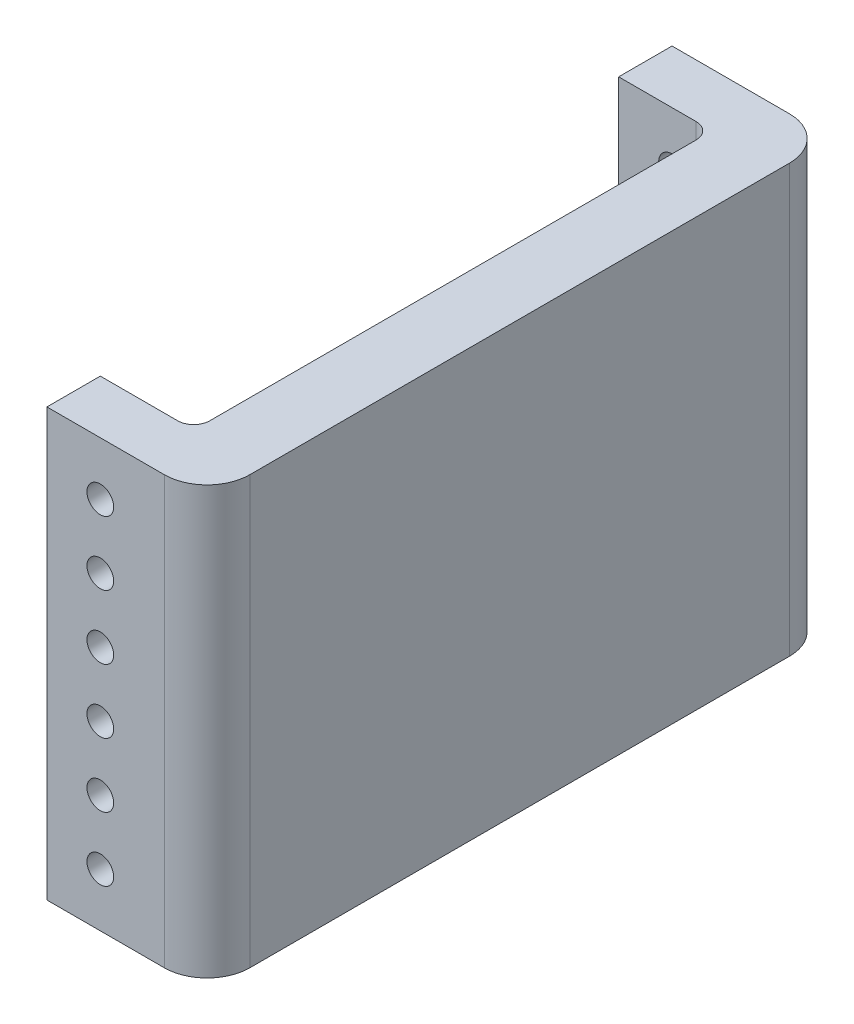
SolidWorks part; units mm, degrees
ref_plane "Front Plane" through (0, 0, 0) normal (0, 0, 1) x (1, 0, 0)
ref_plane "Top Plane" through (0, 0, 0) normal (0, 1, 0) x (1, 0, 0)
ref_plane "Right Plane" through (0, 0, 0) normal (1, 0, 0) x (0, 0, -1)
sketch "Sketch1" plane through (0, 0, 0) normal (1, 0, 0) x (0, 0, -1)
  line L1 (-837.5115, 764.4576) -> (-540.0775, 764.4576)
  line L2 (-837.5115, 764.4576) -> (-837.5115, 561.2576)
  line L3 (-837.5115, 561.2576) -> (-540.0775, 561.2576)
  line L4 (-540.0775, 764.4576) -> (-540.0775, 561.2576)
  dimension "D1" = 297.434
  dimension "D2" = 203.2
extrude "Boss-Extrude1" add sketch "Sketch1" along normal blind 76.2
sketch "Sketch3" plane through (0, 764.4576, 0) normal (0, 1, 0) x (1, 0, 0)
  line L0 (0, -540.0775) -> (0, -837.5115) construction
  line L1 (0, -565.4775) -> (44.45, -565.4775)
  line L2 (0, -565.4775) -> (0, -812.1115)
  line L3 (0, -812.1115) -> (44.45, -812.1115)
  line L4 (44.45, -565.4775) -> (44.45, -812.1115)
  line L5 (76.2, -540.0775) -> (0, -540.0775) construction
  line L6 (76.2, -837.5115) -> (0, -837.5115) construction
  line L7 (76.2, -540.0775) -> (76.2, -837.5115) construction
  dimension "D1" = 25.4
  dimension "D2" = 25.4
  dimension "D3" = 31.75
extrude "Cut-Extrude1" cut sketch "Sketch3" against normal through all
sketch "Sketch4" plane through (0, 0, 837.5115) normal (0, 0, 1) x (1, 0, 0)
  line L0 (76.2, 764.4576) -> (0, 764.4576) construction
  line L1 (0, 764.4576) -> (0, 561.2576) construction
  circle A0 centre (25.4, 739.0576) radius 6.35
  circle A1 centre (25.4, 708.5776) radius 6.35
  circle A2 centre (25.4, 678.0976) radius 6.35
  circle A3 centre (25.4, 647.6176) radius 6.35
  circle A4 centre (25.4, 617.1376) radius 6.35
  circle A5 centre (25.4, 586.6576) radius 6.35
  dimension "D1" = 25.4
  dimension "D2" = 25.4
extrude "Cut-Extrude2" cut sketch "Sketch4" against normal through all
fillet "Fillet1" radius 20.32 2 edges at (76.2, 662.8576, 540.0775) (76.2, 662.8576, 837.5115)
fillet "Fillet2" radius 7.62 2 edges at (44.45, 662.8576, 812.1115) (44.45, 662.8576, 565.4775)
